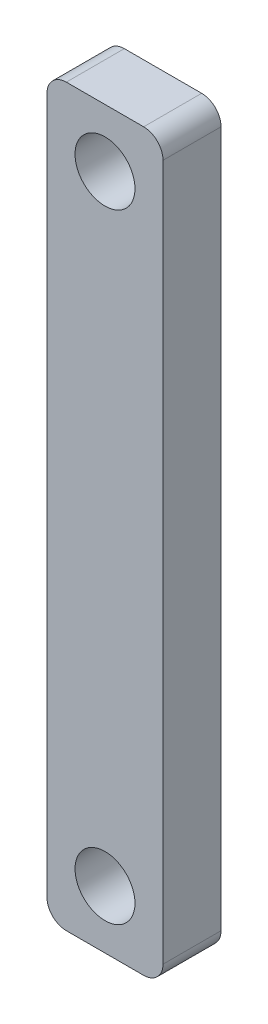
SolidWorks part; units mm, degrees
ref_plane "Plan de face" through (0, 0, 0) normal (0, 0, 1) x (1, 0, 0)
ref_plane "Plan de dessus" through (0, 0, 0) normal (0, 1, 0) x (1, 0, 0)
ref_plane "Plan de droite" through (0, 0, 0) normal (1, 0, 0) x (0, 0, -1)
sketch "Esquisse1" plane through (0, 0, 0) normal (0, 0, 1) x (1, 0, 0)
  line L1 (-3, -19) -> (3, -19)
  line L2 (-3, -19) -> (-3, 19)
  line L3 (-3, 19) -> (3, 19)
  line L4 (3, -19) -> (3, 19)
  line L5 (-3, -19) -> (3, 19) construction
  line L6 (-3, 19) -> (3, -19) construction
  circle A0 centre (0, 16) radius 1.55
  circle A1 centre (0, -16) radius 1.55
  point P0 (0, 0)
  point P10 (0, 19)
  dimension "D3" = 3.1
  dimension "D5" = 3
  dimension "D1" = 6
  dimension "D2" = 38
  dimension "D4" = 3
extrude "Boss.-Extru.1" add sketch "Esquisse1" along normal blind 3
fillet "Congé1" radius 1 4 edges at (-3, -19, 1.5) (3, -19, 1.5) (-3, 19, 1.5) (3, 19, 1.5)
